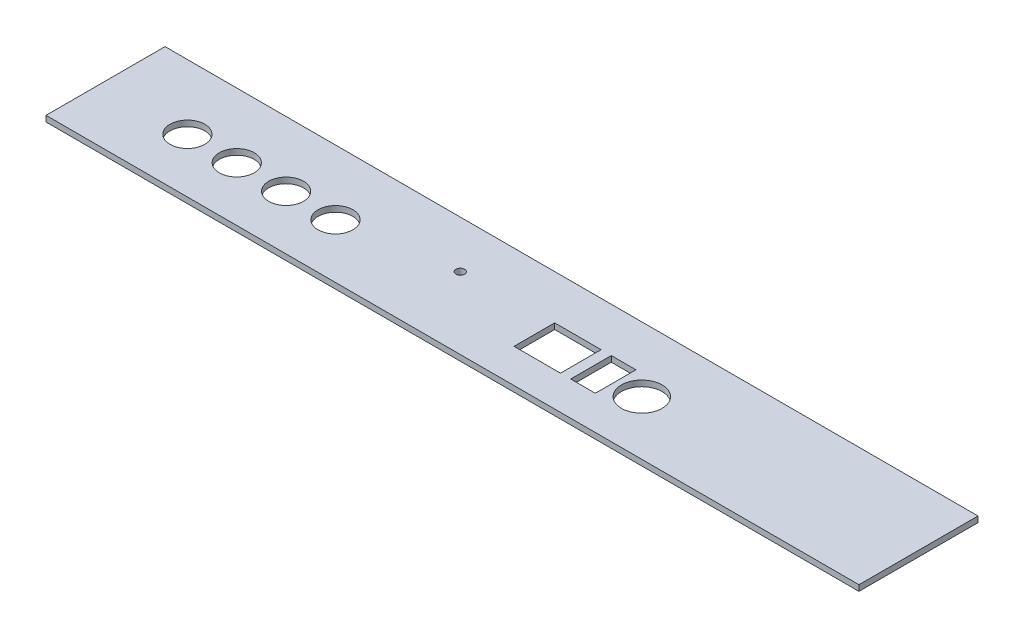
SolidWorks part; units mm, degrees
ref_plane "前视基准面" through (0, 0, 0) normal (0, 0, 1) x (1, 0, 0)
ref_plane "上视基准面" through (0, 0, 0) normal (0, 1, 0) x (1, 0, 0)
ref_plane "右视基准面" through (0, 0, 0) normal (1, 0, 0) x (0, 0, -1)
sketch "草图1" plane through (0, 0, 0) normal (0, 1, 0) x (1, 0, 0)
  line L1 (0, 0) -> (280, 0)
  line L2 (0, 0) -> (0, 41)
  line L3 (0, 41) -> (280, 41)
  line L4 (280, 0) -> (280, 41)
  line L5 (149.5, 11.7) -> (165.5, 11.7)
  line L6 (149.5, 11.7) -> (149.5, 25.7)
  line L7 (149.5, 25.7) -> (165.5, 25.7)
  line L8 (165.5, 11.7) -> (165.5, 25.7)
  line L9 (169, 11.7) -> (177.5, 11.7)
  line L10 (169, 11.7) -> (169, 25.7)
  line L11 (169, 25.7) -> (177.5, 25.7)
  line L12 (177.5, 11.7) -> (177.5, 25.7)
  circle A0 centre (30, 18.7) radius 6
  circle A1 centre (47, 18.7) radius 6
  circle A2 centre (64, 18.7) radius 6
  circle A3 centre (81, 18.7) radius 6
  circle A4 centre (186.5, 18.7) radius 7
  circle A5 centre (118, 24.7) radius 1.5
  dimension "D1" = 4
extrude "凸台-拉伸1" add sketch "草图1" along normal blind 2
